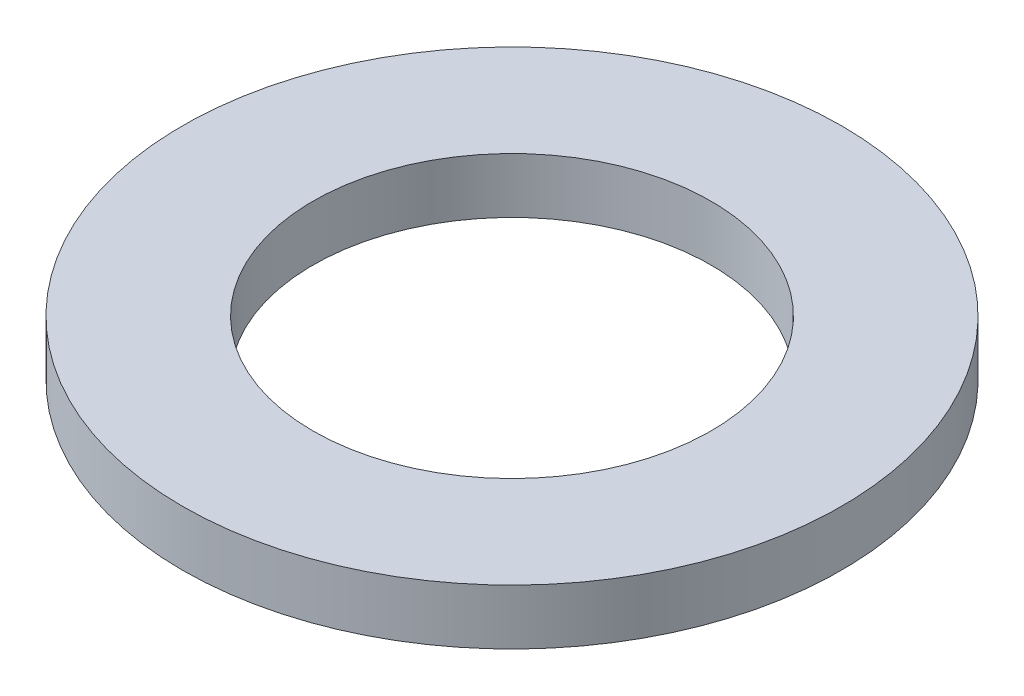
SolidWorks part; units mm, degrees
material "Alloy Steel"
ref_plane "Plane1" through (0, 0, 0) normal (0, 0, 1) x (1, 0, 0)
ref_plane "Plane2" through (0, 0, 0) normal (0, 1, 0) x (1, 0, 0)
ref_plane "Plane3" through (0, 0, 0) normal (1, 0, 0) x (0, 0, -1)
sketch "Sketch2" plane through (0, 0, 0) normal (0, 1, 0) x (1, 0, 0)
  circle A0 centre (0, 0) radius 9.525
  circle A1 centre (0, 0) radius 5.7531
  dimension "ID" = 11.5062
  dimension "OD" = 19.05
extrude "Base-Extrude" add sketch "Sketch2" along normal blind 1.6002
